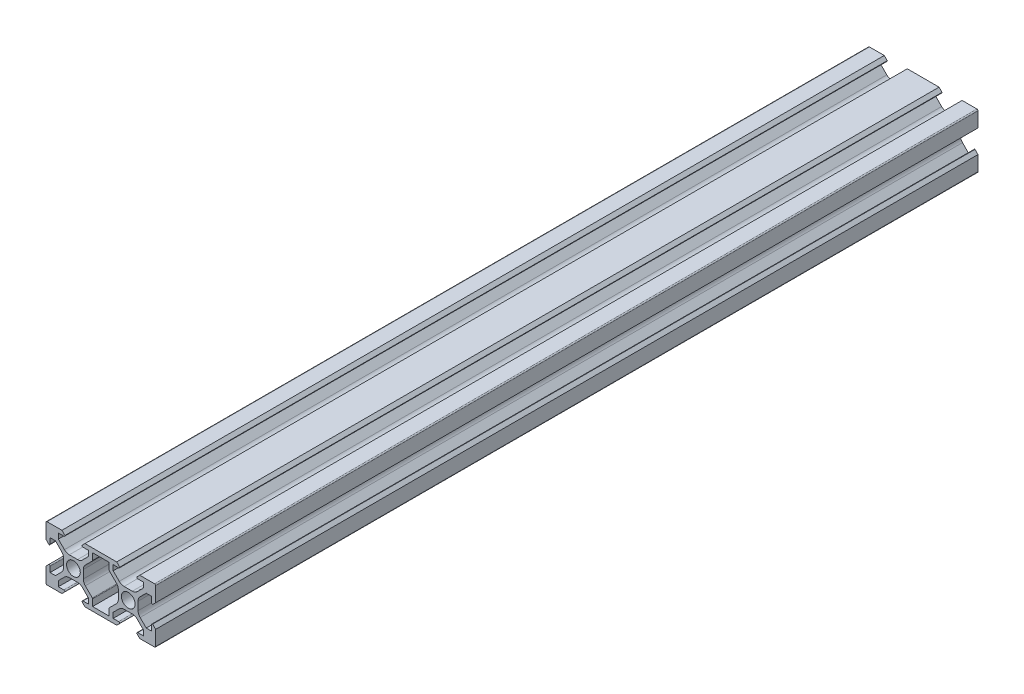
SolidWorks part; units mm, degrees
material "6063-T5"
ref_plane "Plano frontal" through (0, 0, 0) normal (0, 0, 1) x (1, 0, 0)
ref_plane "Plano superior" through (0, 0, 0) normal (0, 1, 0) x (1, 0, 0)
ref_plane "Plano direito" through (0, 0, 0) normal (1, 0, 0) x (0, 0, -1)
sketch "Esboço1" plane through (0, 0, 0) normal (0, 0, 1) x (1, 0, 0)
  line L0 (-13.1, 8.9) -> (-14.2, 10)
  line L1 (-19.6, 10) -> (-14.2, 10)
  line L2 (-13.6, 1.5038) -> (-13.6, 0)
  line L3 (-18.5, 5.5) -> (-18.5, 3.5)
  line L4 (-16.5607, 5.5) -> (-14.3322, 3.2716)
  line L5 (-18.5, 5.5) -> (-16.5607, 5.5)
  line L6 (-20, 9.6) -> (-20, 4.2)
  line L7 (-18.9, 3.1) -> (-20, 4.2)
  line L8 (-3, 8.5) -> (3, 8.5)
  line L9 (-3.1172, 5.8222) -> (-5.6678, 3.2716)
  line L10 (-8.4962, 3.6) -> (-10, 3.6)
  line L11 (-8.2322, 1.7678) -> (-10, 0) construction
  line L12 (-4.5, 6.5607) -> (-6.7284, 4.3322)
  line L13 (-15.5, 8.5) -> (-15.5, 6.5607)
  line L14 (-4.5, 8.5) -> (-4.5, 6.5607)
  line L15 (0, 0) -> (0, 8.5) construction
  line L16 (-6.9, 8.9) -> (-5.8, 10)
  line L17 (-6.4, 0) -> (6.4, 0) construction
  line L18 (-3, -8.5) -> (-3, -6.105)
  line L19 (-18.5, 8.5) -> (-18.5, -8.5) construction
  line L20 (-3.1172, -5.8222) -> (-5.6678, -3.2716)
  line L21 (-6.4, 1.5038) -> (-6.4, 0)
  line L22 (-5.8, -10) -> (5.8, -10)
  line L23 (-19.8828, 9.8828) -> (-10, 0) construction
  line L24 (-6.9, -8.9) -> (-5.8, -10)
  line L25 (-15.5, 6.5607) -> (-13.2716, 4.3322)
  line L26 (-3, -8.5) -> (3, -8.5)
  line L27 (-20, 10) -> (-20, -10) construction
  line L28 (-6.4, -1.5038) -> (-6.4, 0)
  line L29 (19.8828, -9.8828) -> (10, 0) construction
  line L30 (8.2322, -1.7678) -> (10, 0) construction
  line L31 (19.8828, 9.8828) -> (10, 0) construction
  line L32 (8.2322, 1.7678) -> (10, 0) construction
  line L33 (-15.5, 8.5) -> (-13.5, 8.5)
  line L34 (6.5, 8.5) -> (4.5, 8.5)
  line L35 (-4.5, -8.5) -> (-4.5, -6.5607)
  line L36 (-20, 10) -> (0, 10) construction
  line L37 (-4.5, -6.5607) -> (-6.7284, -4.3322)
  line L38 (-4.5, -8.5) -> (-6.5, -8.5)
  line L39 (-18.5, 8.5) -> (-1.5, 8.5) construction
  line L40 (-11.5038, 3.6) -> (-10, 3.6)
  line L41 (-8.4962, -3.6) -> (-10, -3.6)
  line L42 (-8.2322, -1.7678) -> (-10, 0) construction
  line L43 (-18.9, -3.1) -> (-20, -4.2)
  line L44 (-20, -9.6) -> (-20, -4.2)
  line L45 (-11.5038, -3.6) -> (-10, -3.6)
  line L46 (-15.5, -8.5) -> (-13.5, -8.5)
  line L47 (-15.5, -6.5607) -> (-13.2716, -4.3322)
  line L48 (-15.5, -8.5) -> (-15.5, -6.5607)
  line L49 (-19.6, -10) -> (-14.2, -10)
  line L50 (-13.1, -8.9) -> (-14.2, -10)
  line L51 (-18.5, -5.5) -> (-16.5607, -5.5)
  line L52 (-16.5607, -5.5) -> (-14.3322, -3.2716)
  line L53 (-18.5, -5.5) -> (-18.5, -3.5)
  line L54 (0, 10) -> (0, -10) construction
  line L55 (-20, -10) -> (0, -10) construction
  line L56 (-13.6, -1.5038) -> (-13.6, 0)
  line L57 (-18.5, -8.5) -> (-1.5, -8.5) construction
  line L58 (-1.5, 8.5) -> (-1.5, -8.5) construction
  line L59 (-19.8828, -9.8828) -> (-10, 0) construction
  line L60 (3, 8.5) -> (3, 6.105)
  line L61 (-3, 8.5) -> (-3, 6.105)
  line L62 (-6.5, 8.5) -> (-4.5, 8.5)
  line L63 (-5.8, 10) -> (5.8, 10)
  line L64 (13.6, -1.5038) -> (13.6, 0)
  line L65 (18.5, -5.5) -> (18.5, -3.5)
  line L66 (16.5607, -5.5) -> (14.3322, -3.2716)
  line L67 (18.5, -5.5) -> (16.5607, -5.5)
  line L68 (13.1, -8.9) -> (14.2, -10)
  line L69 (19.6, -10) -> (14.2, -10)
  line L70 (15.5, -8.5) -> (15.5, -6.5607)
  line L71 (15.5, -6.5607) -> (13.2716, -4.3322)
  line L72 (15.5, -8.5) -> (13.5, -8.5)
  line L73 (11.5038, -3.6) -> (10, -3.6)
  line L74 (20, -9.6) -> (20, -4.2)
  line L75 (18.9, -3.1) -> (20, -4.2)
  line L76 (8.4962, -3.6) -> (10, -3.6)
  line L77 (11.5038, 3.6) -> (10, 3.6)
  line L78 (4.5, -8.5) -> (6.5, -8.5)
  line L79 (4.5, -6.5607) -> (6.7284, -4.3322)
  line L80 (4.5, -8.5) -> (4.5, -6.5607)
  line L81 (15.5, 8.5) -> (13.5, 8.5)
  line L82 (6.4, -1.5038) -> (6.4, 0)
  line L83 (15.5, 6.5607) -> (13.2716, 4.3322)
  line L84 (6.9, -8.9) -> (5.8, -10)
  line L85 (6.4, 1.5038) -> (6.4, 0)
  line L86 (3.1172, -5.8222) -> (5.6678, -3.2716)
  line L87 (3, -8.5) -> (3, -6.105)
  line L88 (6.9, 8.9) -> (5.8, 10)
  line L89 (4.5, 8.5) -> (4.5, 6.5607)
  line L90 (15.5, 8.5) -> (15.5, 6.5607)
  line L91 (4.5, 6.5607) -> (6.7284, 4.3322)
  line L92 (8.4962, 3.6) -> (10, 3.6)
  line L93 (3.1172, 5.8222) -> (5.6678, 3.2716)
  line L94 (18.9, 3.1) -> (20, 4.2)
  line L95 (20, 9.6) -> (20, 4.2)
  line L96 (18.5, 5.5) -> (16.5607, 5.5)
  line L97 (16.5607, 5.5) -> (14.3322, 3.2716)
  line L98 (18.5, 5.5) -> (18.5, 3.5)
  line L99 (13.6, 1.5038) -> (13.6, 0)
  line L100 (19.6, 10) -> (14.2, 10)
  line L101 (13.1, 8.9) -> (14.2, 10)
  arc A0 (-10, 2.5) -> (-12.5, 0) centre (-10, 0) ccw
  arc A1 (-13.5, 8.5) -> (-13.1, 8.9) centre (-13.5, 8.9) ccw
  arc A2 (-19.6, 10) -> (-20, 9.6) centre (-19.6, 9.6) ccw
  arc A3 (-13.2716, 4.3322) -> (-11.5038, 3.6) centre (-11.5038, 6.1) ccw
  arc A4 (-14.3322, 3.2716) -> (-13.6, 1.5038) centre (-16.1, 1.5038) cw
  arc A5 (-18.5, 3.5) -> (-18.9, 3.1) centre (-18.9, 3.5) cw
  arc A6 (-7.5, 0) -> (-10, 2.5) centre (-10, 0) ccw
  arc A7 (-3, -6.105) -> (-3.1172, -5.8222) centre (-3.4, -6.105) ccw
  arc A8 (-3.1172, 5.8222) -> (-3, 6.105) centre (-3.4, 6.105) ccw
  arc A9 (-5.6678, 3.2716) -> (-6.4, 1.5038) centre (-3.9, 1.5038) ccw
  arc A10 (-6.7284, 4.3322) -> (-8.4962, 3.6) centre (-8.4962, 6.1) cw
  arc A11 (-6.5, 8.5) -> (-6.9, 8.9) centre (-6.5, 8.9) cw
  arc A12 (-10, -2.5) -> (-7.5, 0) centre (-10, 0) ccw
  arc A13 (-6.5, -8.5) -> (-6.9, -8.9) centre (-6.5, -8.9) ccw
  arc A14 (13.5, -8.5) -> (13.1, -8.9) centre (13.5, -8.9) ccw
  arc A15 (-6.7284, -4.3322) -> (-8.4962, -3.6) centre (-8.4962, -6.1) ccw
  arc A16 (-5.6678, -3.2716) -> (-6.4, -1.5038) centre (-3.9, -1.5038) cw
  arc A17 (13.2716, -4.3322) -> (11.5038, -3.6) centre (11.5038, -6.1) ccw
  arc A18 (-12.5, 0) -> (-10, -2.5) centre (-10, 0) ccw
  arc A19 (-18.5, -3.5) -> (-18.9, -3.1) centre (-18.9, -3.5) ccw
  arc A20 (-20, -9.6) -> (-19.6, -10) centre (-19.6, -9.6) ccw
  arc A21 (-14.3322, -3.2716) -> (-13.6, -1.5038) centre (-16.1, -1.5038) ccw
  arc A22 (-13.2716, -4.3322) -> (-11.5038, -3.6) centre (-11.5038, -6.1) cw
  arc A23 (-13.5, -8.5) -> (-13.1, -8.9) centre (-13.5, -8.9) cw
  arc A24 (14.3322, -3.2716) -> (13.6, -1.5038) centre (16.1, -1.5038) cw
  arc A25 (20, -9.6) -> (19.6, -10) centre (19.6, -9.6) cw
  arc A26 (18.5, -3.5) -> (18.9, -3.1) centre (18.9, -3.5) cw
  arc A27 (12.5, 0) -> (10, -2.5) centre (10, 0) cw
  arc A28 (5.6678, -3.2716) -> (6.4, -1.5038) centre (3.9, -1.5038) ccw
  arc A29 (6.7284, -4.3322) -> (8.4962, -3.6) centre (8.4962, -6.1) cw
  arc A30 (6.5, -8.5) -> (6.9, -8.9) centre (6.5, -8.9) cw
  arc A31 (10, -2.5) -> (7.5, 0) centre (10, 0) cw
  arc A32 (6.5, 8.5) -> (6.9, 8.9) centre (6.5, 8.9) ccw
  arc A33 (6.7284, 4.3322) -> (8.4962, 3.6) centre (8.4962, 6.1) ccw
  arc A34 (5.6678, 3.2716) -> (6.4, 1.5038) centre (3.9, 1.5038) cw
  arc A35 (3.1172, 5.8222) -> (3, 6.105) centre (3.4, 6.105) cw
  arc A36 (3, -6.105) -> (3.1172, -5.8222) centre (3.4, -6.105) cw
  arc A37 (7.5, 0) -> (10, 2.5) centre (10, 0) cw
  arc A38 (18.5, 3.5) -> (18.9, 3.1) centre (18.9, 3.5) ccw
  arc A39 (14.3322, 3.2716) -> (13.6, 1.5038) centre (16.1, 1.5038) ccw
  arc A40 (13.2716, 4.3322) -> (11.5038, 3.6) centre (11.5038, 6.1) cw
  arc A41 (19.6, 10) -> (20, 9.6) centre (19.6, 9.6) cw
  arc A42 (13.5, 8.5) -> (13.1, 8.9) centre (13.5, 8.9) cw
  arc A43 (10, 2.5) -> (12.5, 0) centre (10, 0) cw
  point P116 (-10, 0)
  point P168 (0, 10)
  point P183 (0, -8.5)
  point P185 (0, -10)
  dimension "D4" = 2.5
  dimension "D1" = 0.4
  dimension "D3" = 0.4
  dimension "D5" = 0.4
  dimension "D2" = 45
extrude "Ressalto-extrusão1" add sketch "Esboço1" along normal mid plane 300
